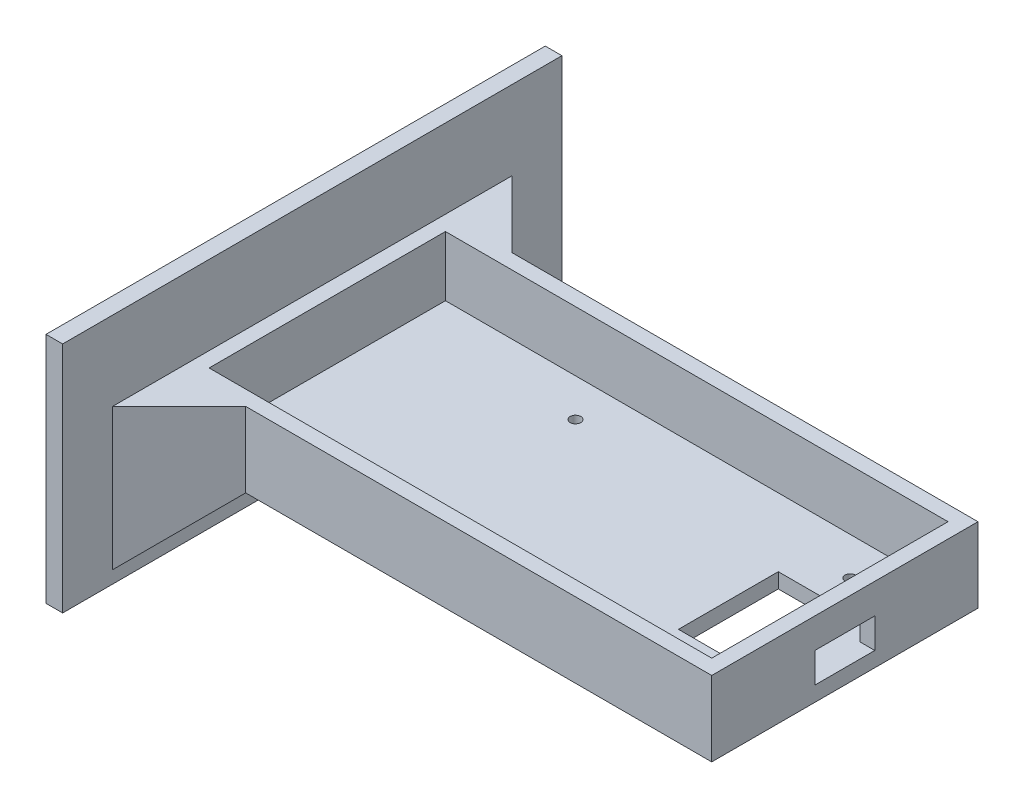
SolidWorks part; units mm, degrees
ref_plane "Front Plane" through (0, 0, 0) normal (0, 0, 1) x (1, 0, 0)
ref_plane "Top Plane" through (0, 0, 0) normal (0, 1, 0) x (1, 0, 0)
ref_plane "Right Plane" through (0, 0, 0) normal (1, 0, 0) x (0, 0, -1)
sketch "Sketch1" plane through (0, 0, 0) normal (0, 1, 0) x (1, 0, 0)
  line L1 (-80, -40) -> (80, -40)
  line L2 (-80, -40) -> (-80, 40)
  line L3 (-80, 40) -> (80, 40)
  line L4 (80, -40) -> (80, 40)
  line L5 (-80, -40) -> (80, 40) construction
  line L6 (-80, 40) -> (80, -40) construction
  point P0 (0, 0)
  dimension "D1" = 160
  dimension "D2" = 80
extrude "Boss-Extrude1" add sketch "Sketch1" along normal blind 22.5 contours L2 L3 L4 L1
sketch "Sketch2" plane through (0, 22.5, 0) normal (0, 1, 0) x (1, 0, 0)
  line L1 (-75.5, -35.5) -> (75.5, -35.5)
  line L2 (-75.5, -35.5) -> (-75.5, 35.5)
  line L3 (-75.5, 35.5) -> (75.5, 35.5)
  line L4 (75.5, -35.5) -> (75.5, 35.5)
  line L5 (-75.5, -35.5) -> (75.5, 35.5) construction
  line L6 (-75.5, 35.5) -> (75.5, -35.5) construction
  point P0 (0, 0)
  dimension "D1" = 71
  dimension "D2" = 151
extrude "Cut-Extrude1" cut sketch "Sketch2" against normal blind 18 contours L3 L4 L1 L2
sketch "Sketch3" plane through (-80, 0, 0) normal (-1, 0, 0) x (0, 0, 1)
  line L0 (40, 22.5) -> (-40, 22.5) construction
  line L1 (-75, -23.75) -> (75, -23.75)
  line L2 (-75, -23.75) -> (-75, 46.25)
  line L3 (-75, 46.25) -> (75, 46.25)
  line L4 (75, -23.75) -> (75, 46.25)
  line L5 (-75, -23.75) -> (75, 46.25) construction
  line L6 (-75, 46.25) -> (75, -23.75) construction
  line L9 (-40, 22.5) -> (-40, 0) construction
  point P0 (0, 11.25)
  dimension "D1" = 11.25
  dimension "D2" = 40
  dimension "D3" = 150
  dimension "D4" = 70
extrude "Boss-Extrude2" add sketch "Sketch3" along normal blind 5
sketch "Sketch4" plane through (80, 0, 0) normal (1, 0, 0) x (0, 0, -1)
  line L1 (-9, 13.5) -> (9, 13.5)
  line L2 (-9, 13.5) -> (-9, 4.5)
  line L3 (-9, 4.5) -> (9, 4.5)
  line L4 (9, 13.5) -> (9, 4.5)
  line L5 (-40, 22.5) -> (-40, 0) construction
  line L7 (-40, 0) -> (40, 0) construction
  dimension "D1" = 18
  dimension "D2" = 9
  dimension "D3" = 31
  dimension "D4" = 4.5
extrude "Cut-Extrude3" cut sketch "Sketch4" against normal blind 13 contours L1 L4 L3 L2
sketch "Sketch6" plane through (0, 4.5, 0) normal (0, 1, 0) x (1, 0, 0)
  line L0 (75.5, -35.5) -> (75.5, -9) construction
  line L1 (-75.5, 35.5) -> (75.5, 35.5) construction
  line L2 (75.5, -35.5) -> (75.5, 35.5) construction
  circle A0 centre (57.5, 24.14) radius 1.6
  circle A1 centre (56.23, -24.12) radius 1.6
  circle A2 centre (-18.7, -24.14) radius 1.6
  circle A3 centre (-25.05, 24.12) radius 1.6
  point P14 (0, 0)
  point P15 (0, 0)
  dimension "D1" = 48.26
  dimension "D3" = 74.93
  dimension "D4" = 19.27
  dimension "D2" = 11.36
  dimension "D5" = 48.26
  dimension "D6" = 18
  dimension "D7" = 82.55
extrude "Cut-Extrude5" cut sketch "Sketch6" against normal blind 13
sketch "Sketch5" plane through (0, 0, 0) normal (0, -1, 0) x (1, 0, 0)
  line L0 (80, 40) -> (80, -40) construction
  line L1 (45, 15) -> (70, 15)
  line L2 (45, 15) -> (45, -15)
  line L3 (45, -15) -> (70, -15)
  line L4 (70, 15) -> (70, -15)
  line L5 (-80, -40) -> (80, -40) construction
  dimension "D1" = 10
  dimension "D2" = 30
  dimension "D3" = 25
  dimension "D4" = 25
extrude "Cut-Extrude6" cut sketch "Sketch5" against normal blind 13
chamfer "Chamfer3" distance 20 angle 45 3 edges at (-80, 11.25, 40) (-80, 0, 0) (-80, 11.25, -40)
